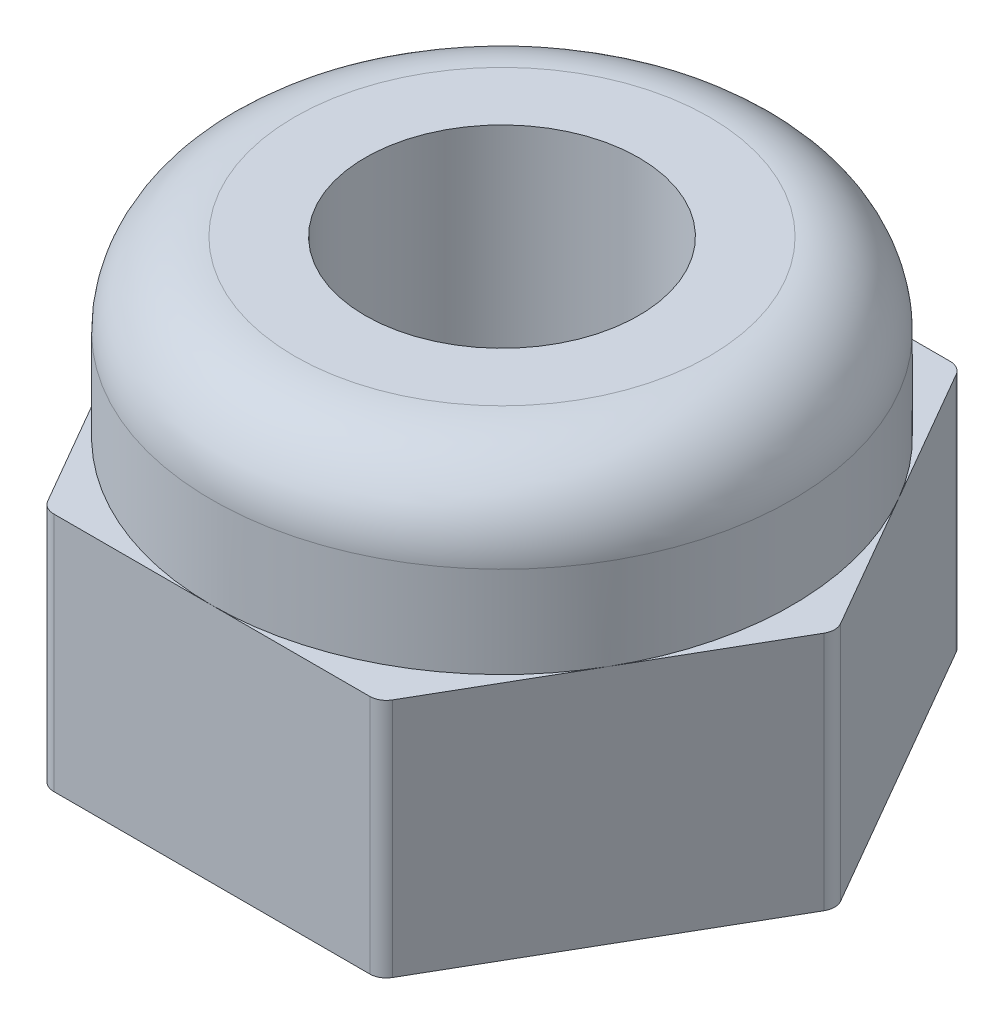
SolidWorks part; units mm, degrees
ref_plane "Front Plane" through (0, 0, 0) normal (0, 0, 1) x (1, 0, 0)
ref_plane "Top Plane" through (0, 0, 0) normal (0, 1, 0) x (1, 0, 0)
ref_plane "Right Plane" through (0, 0, 0) normal (1, 0, 0) x (0, 0, -1)
sketch "Sketch1" plane through (0, 0, 0) normal (0, 1, 0) x (1, 0, 0)
  line L1 (4.0415, 0) -> (2.0207, 3.5)
  line L2 (2.0207, 3.5) -> (-2.0207, 3.5)
  line L3 (-2.0207, 3.5) -> (-4.0415, 0)
  line L4 (-4.0415, 0) -> (-2.0207, -3.5)
  line L5 (-2.0207, -3.5) -> (2.0207, -3.5)
  line L6 (2.0207, -3.5) -> (4.0415, 0)
  circle A0 centre (0, 0) radius 3.5 construction
  dimension "D1" = 7
extrude "Boss-Extrude1" add sketch "Sketch1" along normal blind 2.9
sketch "Sketch2" plane through (0, 0, 0) normal (0, -1, 0) x (1, 0, 0)
  line L0 (-2.0207, 3.5) -> (2.0207, 3.5) construction
  circle A0 centre (0, 0) radius 3.5
extrude "Boss-Extrude2" add sketch "Sketch2" against normal blind 5
fillet "Fillet1" radius 1 1 edges at (0, 5, -3.5)
fillet "Fillet2" radius 0.2 6 edges at (-2.0207, 1.45, 3.5) (-4.0415, 1.45, 0) (-2.0207, 1.45, -3.5) (2.0207, 1.45, -3.5) (4.0415, 1.45, 0) (2.0207, 1.45, 3.5)
hole_wizard "M4 Tapped Hole1" positions "Sketch3" profile "Sketch5" tap size "M4" standard "GB" end condition through all
sketch "Sketch3" plane through (0, 0, 0) normal (0, -1, 0) x (-1, 0, 0)
  point P0 (0, 0)
sketch "Sketch5" plane through (0, 0, 0) normal (1, 0, 0) x (0, 0, -1)
  line L0 (0, 0) -> (0, 5)
  line L1 (0, 5) -> (1.65, 5)
  line L2 (1.65, 5) -> (1.65, 0)
  line L5 (1.65, 0) -> (0, 0)
  line L11 (0, -6.35) -> (0, 107.95) construction
  dimension "Thru Tap Drill Dia." = 3.3
  dimension "Thru Tap Drill Depth" = 5
cosmetic thread "Hole Thread1" parameters "D2"=4
